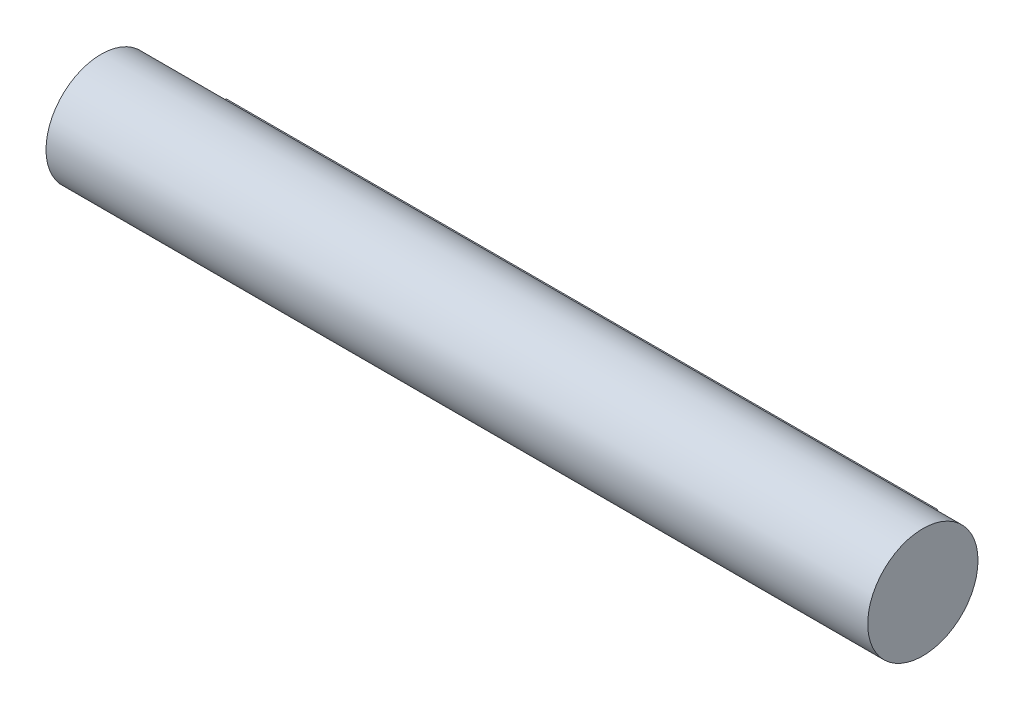
SolidWorks part; units mm, degrees
ref_plane "Front Plane" through (0, 0, 0) normal (0, 0, 1) x (1, 0, 0)
ref_plane "Top Plane" through (0, 0, 0) normal (0, 1, 0) x (1, 0, 0)
ref_plane "Right Plane" through (0, 0, 0) normal (1, 0, 0) x (0, 0, -1)
sketch "Sketch1" plane through (0, 0, 0) normal (1, 0, 0) x (0, 0, -1)
  line L1 (27.94, -6.35) -> (48.26, -6.35)
  line L2 (27.94, -6.35) -> (27.94, 6.35)
  line L3 (27.94, 6.35) -> (48.26, 6.35)
  line L4 (48.26, -6.35) -> (48.26, 6.35)
  line L5 (27.94, -6.35) -> (48.26, 6.35) construction
  line L6 (27.94, 6.35) -> (48.26, -6.35) construction
  circle A0 centre (0, 0) radius 38.1
  point P3 (38.1, 0)
  dimension "D1" = 76.2
  dimension "D2" = 20.32
  dimension "D3" = 12.7
extrude "Boss-Extrude1" add sketch "Sketch1" against normal blind 491.49 contours L3 A0 L1 L2 | A0 L1 L4 L3 | L1 A0 L3 L2
sketch "Sketch2" plane through (0, 0, 0) normal (1, 0, 0) x (0, 0, -1)
  circle A0 centre (0, 0) radius 38.1
  point P0 (0, 0)
extrude "Boss-Extrude2" add sketch "Sketch2" along normal blind 38.1
sketch "Sketch3" plane through (-491.49, 0, 0) normal (-1, 0, 0) x (0, 0, 1)
  circle A0 centre (0, 0) radius 38.1
extrude "Boss-Extrude3" add sketch "Sketch3" along normal blind 38.1
